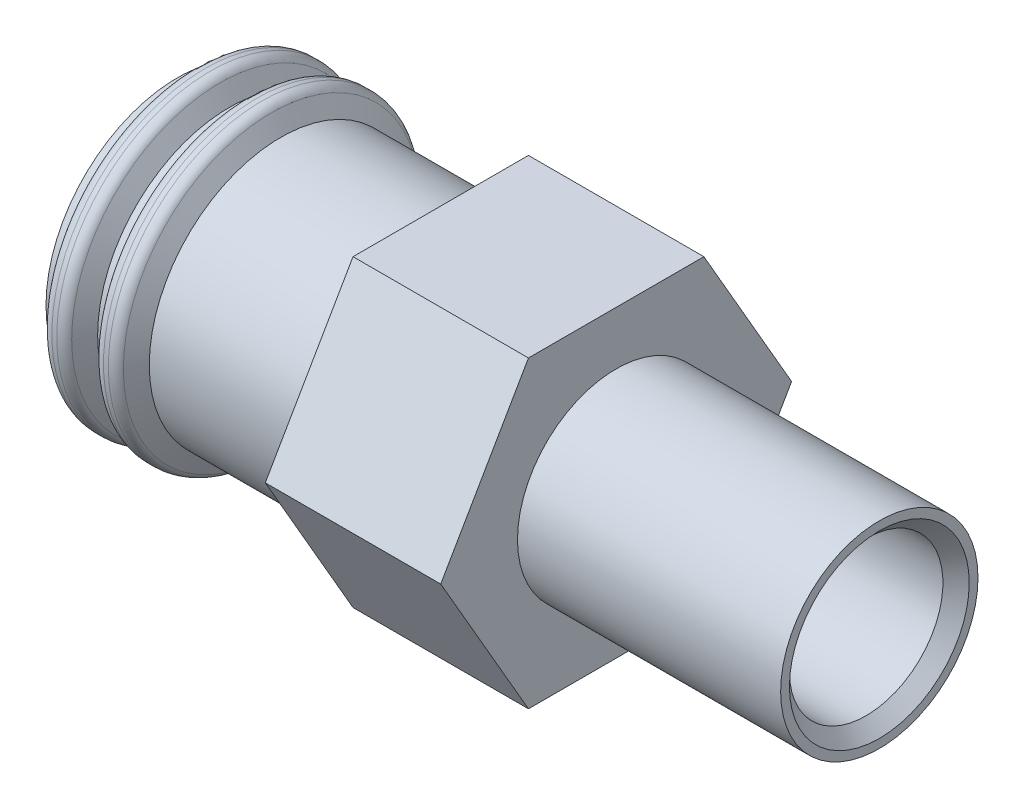
SolidWorks part; units mm, degrees
ref_plane "Plano frontal" through (0, 0, 0) normal (0, 0, 1) x (1, 0, 0)
ref_plane "Plano superior" through (0, 0, 0) normal (0, 1, 0) x (1, 0, 0)
ref_plane "Plano direito" through (0, 0, 0) normal (1, 0, 0) x (0, 0, -1)
sketch "Esboço1" plane through (0, 0, 0) normal (0, 0, 1) x (1, 0, 0)
  line L0 (-29.7219, 0) -> (34.3685, 0) construction
  line L1 (-7.3226, 3) -> (-7.1226, 3)
  line L2 (-2.5, 3) -> (-2.5, 4)
  line L3 (-2.5, 4) -> (1.5, 4)
  line L4 (1.5, 4) -> (1.5, 2.25)
  line L5 (1.5, 2.25) -> (7.5, 2.25)
  line L6 (7.5, 2.25) -> (7.5, 1.75)
  line L7 (-8.0113, 3.5) -> (-8.3, 3)
  line L8 (-8.5, 2.5) -> (-8.5, 3)
  line L9 (-4.5, 2.5) -> (-8.5, 2.5)
  line L10 (-3.201, 1.75) -> (7.5, 1.75)
  line L11 (-8.5, 2.5) -> (8.7174, 2.5) construction
  line L12 (0, 4) -> (0, 1.75) construction
  line L13 (0, 0) -> (0, 4.9732) construction
  line L14 (-4.5, 2.5) -> (-3.201, 1.75)
  line L15 (-8.0113, 3.5) -> (-7.6113, 3.5)
  line L16 (-7.6113, 3.5) -> (-7.3226, 3)
  line L17 (-7.1226, 3) -> (-6.834, 3.5)
  line L18 (-6.834, 3.5) -> (-6.434, 3.5)
  line L19 (-6.434, 3.5) -> (-6.1453, 3)
  line L20 (-6.1453, 3) -> (-2.5, 3)
  line L21 (-8.5, 3) -> (-8.3, 3)
  dimension "D12" = 60
  dimension "D1" = 5
  dimension "D2" = 4.5
  dimension "D3" = 0.5
  dimension "D4" = 16
  dimension "D5" = 8
  dimension "D6" = 6
  dimension "D7" = 4
  dimension "D8" = 4
  dimension "D9" = 6
  dimension "D10" = 7.5
  dimension "D11" = 150
  dimension "D13" = 60
  dimension "D14" = 0.5
  dimension "D15" = 0.5
  dimension "D16" = 0.4
  dimension "D17" = 0.2
  dimension "D18" = 60
  dimension "D19" = 60
  dimension "D20" = 0.5
  dimension "D21" = 0.4
  dimension "D22" = 0.2
revolve "Revolução1" add sketch "Esboço1" angle 360 about L0
sketch "Esboço2" plane through (1.5, 0, 0) normal (1, 0, 0) x (0, 0, -1)
  line L1 (4, 0) -> (2, 3.4641)
  line L2 (2, 3.4641) -> (-2, 3.4641)
  line L3 (-2, 3.4641) -> (-4, 0)
  line L4 (-4, 0) -> (-2, -3.4641)
  line L5 (-2, -3.4641) -> (2, -3.4641)
  line L6 (2, -3.4641) -> (4, 0)
  circle A0 centre (0, 0) radius 3.4641 construction
  circle A1 centre (0, 0) radius 4
  circle M2 centre (0, 0) radius 4
  dimension "D1" = 4
extrude "Corte-extrusão1" cut sketch "Esboço2" against normal blind 4 contours L2 M2 | L3 M2 | L4 M2 | L5 M2 | L6 M2 | L1 M2
fillet "Filete1" radius 0.25 2 edges at (-7.6113, 0, 3.5) (-8.0113, 0, 3.5)
fillet "Filete2" radius 0.25 2 edges at (-6.834, 0, 3.5) (-6.434, 0, 3.5)
chamfer "Chanfro1" distance 0.3 angle 45 1 edges at (7.5, 0, 1.75)
